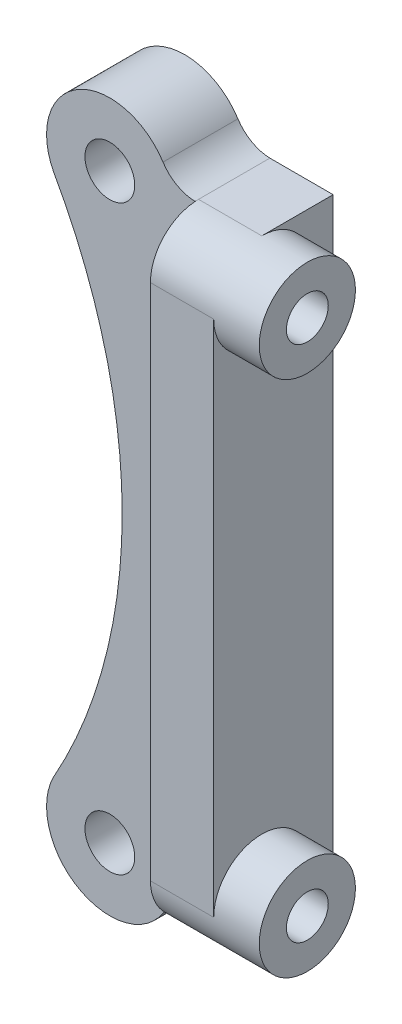
SolidWorks part; units mm, degrees
material "7079 Alloy"
ref_plane "Front Plane" through (0, 0, 0) normal (0, 0, 1) x (1, 0, 0)
ref_plane "Top Plane" through (0, 0, 0) normal (0, 1, 0) x (1, 0, 0)
ref_plane "Right Plane" through (0, 0, 0) normal (1, 0, 0) x (0, 0, -1)
sketch "Sketch1" plane through (0, 0, 0) normal (1, 0, 0) x (0, 0, -1)
  line L0 (17.907, -77.0636) -> (17.907, 77.0636)
  line L1 (17.907, 77.0636) -> (0, 77.0636)
  line L2 (17.907, -77.0636) -> (0, -77.0636)
  line L3 (-12.065, -64.9986) -> (-12.065, 64.9986)
  arc A0 (0, 77.0636) -> (-12.065, 64.9986) centre (0, 64.9986) ccw
  arc A1 (0, -77.0636) -> (-12.065, -64.9986) centre (0, -64.9986) cw
extrude "Extrude1" add sketch "Sketch1" along normal blind 15.875
sketch "Sketch2" plane through (15.875, 0, 0) normal (1, 0, 0) x (0, 0, -1)
  circle A0 centre (0, 64.9986) radius 12.065
extrude "Extrude2" add sketch "Sketch2" along normal blind 11.43
mirror "Mirror of Extrude 2" about plane through (0, 0, 0) normal (0, 1, 0) of "Extrude2"
sketch "Sketch4" plane through (0, 0, -17.907) normal (0, 0, -1) x (-1, 0, 0)
  line L0 (152.4, 0) -> (-137.5255, 0) construction
  line L1 (0, 77.0636) -> (0, -77.0636)
  line L2 (21.3614, 72.9996) -> (21.3614, -72.9996) construction
  arc A0 (7.8567, -81.3445) -> (35.4881, -65.7572) centre (21.3614, -72.9996) ccw
  arc A1 (35.4881, 65.7572) -> (8.0155, 81.5962) centre (21.3614, 72.9996) ccw
  arc A2 (35.4881, 65.7572) -> (35.4881, -65.7572) centre (152.4, 0) ccw
  arc A3 (0, 77.0636) -> (8.0155, 81.5962) centre (-0.3042, 86.9552) ccw
  arc A4 (0, -77.0636) -> (8.0155, -81.5962) centre (-0.3042, -86.9552) cw
  point P5 (18.2642, 0)
  point P9 (0, 0)
extrude "Extrude4" add sketch "Sketch4" against normal blind 18.796
sketch "Sketch5" plane through (0, 0, 0.889) normal (0, 0, 1) x (1, 0, 0)
  circle A0 centre (-21.3614, 72.9996) radius 6.2484
extrude "Cut-Extrude1" cut sketch "Sketch5" against normal through all
sketch "Sketch7" plane through (27.305, 0, 0) normal (1, 0, 0) x (0, 0, -1)
  circle A0 centre (0, 64.9986) radius 5.2502
extrude "Cut-Extrude2" cut sketch "Sketch7" against normal blind 25.4
mirror "Mirror1" about plane through (0, 0, 0) normal (0, 1, 0) of "Cut-Extrude2", "Cut-Extrude1"
